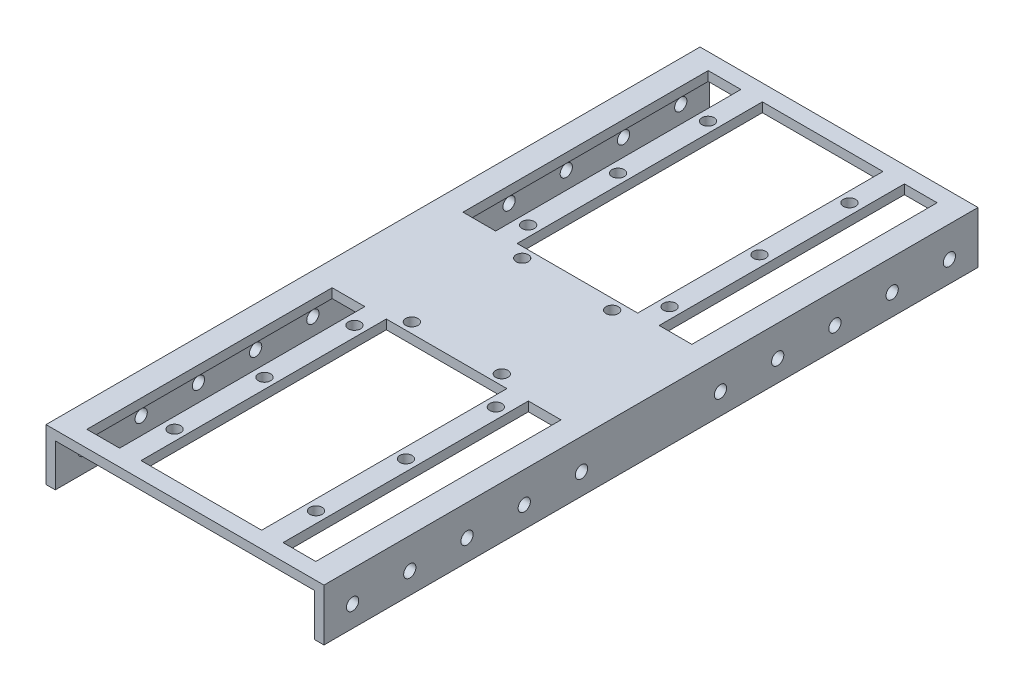
SolidWorks part; units mm, degrees
ref_plane "Front Plane" through (0, 0, 0) normal (0, 0, 1) x (1, 0, 0)
ref_plane "Top Plane" through (0, 0, 0) normal (0, 1, 0) x (1, 0, 0)
ref_plane "Right Plane" through (0, 0, 0) normal (1, 0, 0) x (0, 0, -1)
sketch "Sketch1" plane through (0, 0, 0) normal (0, 0, 1) x (1, 0, 0)
  line L0 (-72.9597, 0) -> (85.1196, 0) construction
  line L1 (0, -62.9989) -> (0, 59.8942) construction
  line L2 (-34, 17.9812) -> (34, 17.9812)
  line L3 (34, 17.9812) -> (34, 5.2812)
  line L4 (34, 5.2812) -> (31.715, 5.2812)
  line L5 (31.715, 5.2812) -> (31.715, 15.6812)
  line L6 (31.715, 15.6812) -> (-31.715, 15.6812)
  line L7 (-31.715, 15.6812) -> (-31.715, 5.2812)
  line L8 (-34, 17.9812) -> (-34, 5.2812)
  line L9 (-34, 5.2812) -> (-31.715, 5.2812)
  point P11 (0, 0)
  point P14 (0, 0)
  point P15 (0, 0)
  point P16 (0, 0)
  point P17 (0, 0)
  dimension "D1" = 68
  dimension "D2" = 12.7
  dimension "D3" = 10.4
  dimension "D4" = 63.43
extrude "Boss-Extrude1" add sketch "Sketch1" along normal mid plane 160
sketch "Sketch2" plane through (0, 17.9812, 0) normal (0, 1, 0) x (1, 0, 0)
  line L0 (0, 0) -> (0, 86.1742) construction
  line L1 (-28, 76) -> (-20, 76)
  line L2 (-28, 76) -> (-28, 16)
  line L3 (-28, 16) -> (-20, 16)
  line L4 (-20, 76) -> (-20, 16)
  line L5 (-14.75, 76) -> (14.75, 76)
  line L6 (-14.75, 76) -> (-14.75, 16)
  line L7 (-14.75, 16) -> (14.75, 16)
  line L8 (14.75, 76) -> (14.75, 16)
  line L9 (20, 76) -> (28, 76)
  line L10 (20, 76) -> (20, 16)
  line L11 (20, 16) -> (28, 16)
  line L12 (28, 76) -> (28, 16)
  line L13 (34, 80) -> (-34, 80) construction
  line L14 (-34, -80) -> (-34, 80) construction
  line L16 (0, 0) -> (114.7578, 0) construction
  line L17 (20, -16) -> (28, -16)
  line L18 (28, -76) -> (28, -16)
  line L19 (20, -76) -> (28, -76)
  line L20 (20, -76) -> (20, -16)
  line L21 (-14.75, -16) -> (14.75, -16)
  line L22 (14.75, -76) -> (14.75, -16)
  line L23 (-14.75, -76) -> (14.75, -76)
  line L24 (-14.75, -76) -> (-14.75, -16)
  line L25 (-28, -16) -> (-20, -16)
  line L26 (-20, -76) -> (-20, -16)
  line L27 (-28, -76) -> (-20, -76)
  line L28 (-28, -76) -> (-28, -16)
  dimension "D1" = 4
  dimension "D2" = 6
  dimension "D3" = 64
  dimension "D4" = 5.25
  dimension "D5" = 8
extrude "Cut-Extrude1" cut sketch "Sketch2" against normal blind 160
sketch "Sketch3" plane through (0, 17.9812, 0) normal (0, 1, 0) x (1, 0, 0)
  line L0 (0, 0) -> (0, 86.1742) construction
  line L1 (0, 0) -> (114.7578, 0) construction
  line L2 (-14.75, 16) -> (14.75, 16) construction
  line L3 (34, 80) -> (-34, 80) construction
  circle A0 centre (-17.3, 65.25) radius 1.5
  circle A1 centre (-11, 13.5) radius 1.5
  circle A2 centre (17.3, 65.25) radius 1.5
  circle A3 centre (17.3, 43.25) radius 1.5
  circle A4 centre (17.3, 21.25) radius 1.5
  circle A5 centre (-17.3, 43.25) radius 1.5
  circle A6 centre (-17.3, 21.25) radius 1.5
  circle A7 centre (11, 13.5) radius 1.5
  circle A8 centre (17.3, -65.25) radius 1.5
  circle A9 centre (17.3, -43.25) radius 1.5
  circle A10 centre (17.3, -21.25) radius 1.5
  circle A11 centre (11, -13.5) radius 1.5
  circle A12 centre (-11, -13.5) radius 1.5
  circle A13 centre (-17.3, -21.25) radius 1.5
  circle A14 centre (-17.3, -43.25) radius 1.5
  circle A15 centre (-17.3, -65.25) radius 1.5
  dimension "D1" = 3
  dimension "D2" = 3
  dimension "D3" = 17.3
  dimension "D4" = 2.5
  dimension "D5" = 14.75
  dimension "D9" = 11
  dimension "D6" = 2
  dimension "D7" = 3
  dimension "D8" = 2
extrude "Cut-Extrude2" cut sketch "Sketch3" against normal blind 160
sketch "Sketch4" plane through (-34, 0, 0) normal (-1, 0, 0) x (0, 0, 1)
  line L0 (-80, 17.9812) -> (-80, 5.2812) construction
  line L1 (80, 5.2812) -> (-80, 5.2812) construction
  point P0 (-73, 10.4812)
  point P5 (0, 0)
  point P6 (0, 0)
  point P7 (0, 0)
  point P8 (0, 0)
  dimension "D1" = 7
  dimension "D2" = 5.2
hole_wizard "Ø3.0mm Dowel Hole1" positions "3DSketch2" profile "Sketch5" hole size "Ø3.0" standard "ISO" end condition through all
sketch3d "3DSketch2"
  point P0 (-34, 10.4812, -73)
sketch "Sketch5" plane through (-34, 10.4812, -73) normal (0, 1, 0) x (0, 0, 1)
  line L0 (0, 0) -> (0, 68)
  line L1 (0, 68) -> (1.5, 68)
  line L2 (1.5, 68) -> (1.5, 0)
  line L5 (1.5, 0) -> (0, 0)
  line L11 (0, -6.35) -> (0, 107.95) construction
  dimension "Thru Hole Dia." = 3
  dimension "Thru Hole Depth" = 68
pattern_linear "LPattern1" count 5 spacing 14 along (0, 0, 1) of "Ø3.0mm Dowel Hole1"
sketch "Sketch6" plane through (-34, 0, 0) normal (-1, 0, 0) x (0, 0, 1)
  line L0 (80, 5.2812) -> (-80, 5.2812) construction
  line L1 (80, 17.9812) -> (80, 5.2812) construction
  point P0 (73, 10.4812)
  dimension "D1" = 5.2
  dimension "D2" = 7
hole_wizard "Ø3.0mm Dowel Hole2" positions "3DSketch3" profile "Sketch7" hole size "Ø3.0" standard "ISO" end condition through all
sketch3d "3DSketch3"
  point P0 (-34, 10.4812, 73)
sketch "Sketch7" plane through (-34, 10.4812, 73) normal (0, 1, 0) x (0, 0, 1)
  line L0 (0, 0) -> (0, 68)
  line L1 (0, 68) -> (1.5, 68)
  line L2 (1.5, 68) -> (1.5, 0)
  line L5 (1.5, 0) -> (0, 0)
  line L11 (0, -6.35) -> (0, 107.95) construction
  dimension "Thru Hole Dia." = 3
  dimension "Thru Hole Depth" = 68
pattern_linear "LPattern2" count 5 spacing 14 along (0, 0, -1) of "Ø3.0mm Dowel Hole2"
